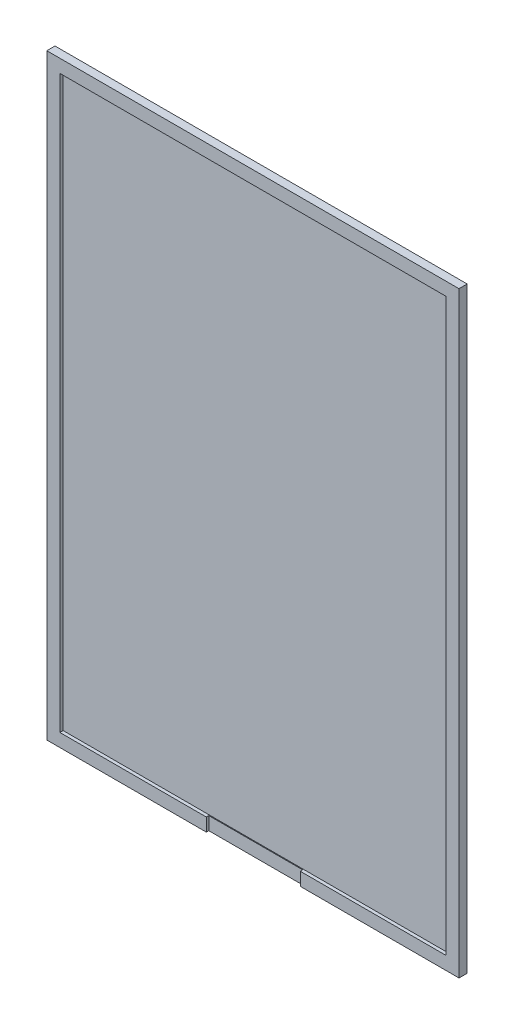
SolidWorks part; units mm, degrees
ref_plane "Alzado" through (0, 0, 0) normal (0, 0, 1) x (1, 0, 0)
ref_plane "Planta" through (0, 0, 0) normal (0, 1, 0) x (1, 0, 0)
ref_plane "Vista lateral" through (0, 0, 0) normal (1, 0, 0) x (0, 0, -1)
sketch "Croquis1" plane through (0, 0, 0) normal (0, 0, 1) x (1, 0, 0)
  line L1 (25.2, -36.5) -> (-25.2, -36.5)
  line L2 (25.2, -36.5) -> (25.2, 36.5)
  line L3 (25.2, 36.5) -> (-25.2, 36.5)
  line L4 (-25.2, -36.5) -> (-25.2, 36.5)
  line L5 (25.2, -36.5) -> (-25.2, 36.5) construction
  line L6 (25.2, 36.5) -> (-25.2, -36.5) construction
  point P0 (0, 0)
  dimension "D1" = 73
  dimension "D2" = 50.4
extrude "Saliente-Extruir1" add sketch "Croquis1" along normal blind 1
ref_plane "Plano1" through (0, 0, 1) normal (0, 0, 1) x (1, 0, 0)
sketch "Croquis2" plane through (0, 0, 1) normal (0, 0, 1) x (1, 0, 0)
  line L0 (-25.2, 36.5) -> (-25.2, -36.5) construction
  line L1 (23.6, -34.9) -> (-23.6, -34.9)
  line L2 (23.6, -34.9) -> (23.6, 34.9)
  line L3 (23.6, 34.9) -> (-23.6, 34.9)
  line L4 (-23.6, -34.9) -> (-23.6, 34.9)
  line L5 (23.6, -34.9) -> (-23.6, 34.9) construction
  line L6 (23.6, 34.9) -> (-23.6, -34.9) construction
  line L7 (-25.2, -36.5) -> (25.2, -36.5) construction
  point P0 (0, 0)
  dimension "D1" = 1.6
  dimension "D2" = 1.6
extrude "Cortar-Extruir1" cut sketch "Croquis2" against normal blind 0.4
ref_plane "Plano2" through (0, 0, 1.6) normal (0, 0, 1) x (1, 0, 0)
sketch "Croquis3" plane through (0, 0, 1.6) normal (0, 0, 1) x (1, 0, 0)
  line L0 (-23.6, -34.9) -> (-5.7, -34.9) construction
  line L1 (-23.6, -34.9) -> (23.6, -34.9) construction
  line L2 (-5.7, -34.9) -> (5.8, -34.9)
  line L3 (-23.6, -34.9) -> (23.6, -34.9) construction
  line L4 (5.8, -34.9) -> (5.8, -36.5)
  line L5 (-25.2, -36.5) -> (25.2, -36.5) construction
  line L6 (5.8, -36.5) -> (-5.7, -36.5)
  line L7 (-5.7, -36.5) -> (-5.7, -34.9)
  dimension "D1" = 17.9
  dimension "D2" = 11.5
extrude "Cortar-Extruir2" cut sketch "Croquis3" against normal blind 0.9
